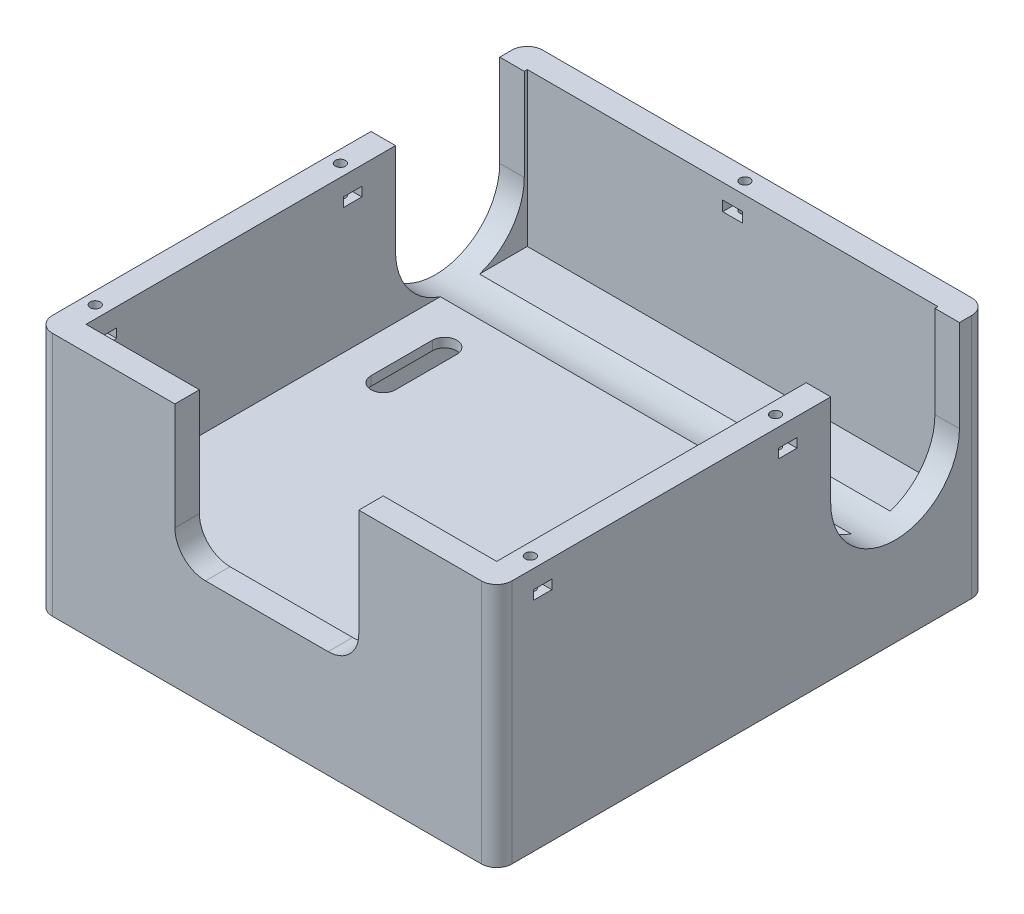
SolidWorks part; units mm, degrees
ref_plane "前视基准面" through (0, 0, 0) normal (0, 0, 1) x (1, 0, 0)
ref_plane "上视基准面" through (0, 0, 0) normal (0, 1, 0) x (1, 0, 0)
ref_plane "右视基准面" through (0, 0, 0) normal (1, 0, 0) x (0, 0, -1)
sketch "草图1" plane through (0, 0, 0) normal (0, 1, 0) x (1, 0, 0)
  line L1 (-75, 80) -> (75, 80)
  line L2 (-75, 80) -> (-75, -80)
  line L3 (-75, -80) -> (75, -80)
  line L4 (75, 80) -> (75, -80)
  line L5 (-75, 80) -> (75, -80) construction
  line L6 (-75, -80) -> (75, 80) construction
  point P0 (0, 0)
  dimension "D1" = 150
  dimension "D2" = 160
extrude "凸台-拉伸1" add sketch "草图1" along normal blind 80
sketch "草图2" plane through (-75, 0, 0) normal (-1, 0, 0) x (0, 0, 1)
  line L0 (-80, 80) -> (-80, 0) construction
  line L1 (-29, 50) -> (-29, 80)
  line L2 (-80, 80) -> (80, 80) construction
  line L3 (-29, 80) -> (-71, 80)
  line L4 (-71, 80) -> (-71, 50)
  arc A0 (-71, 50) -> (-29, 50) centre (-50, 50) ccw
  dimension "D1" = 42
  dimension "D2" = 30
  dimension "D3" = 30
extrude "切除-拉伸1" cut sketch "草图2" against normal through all
fillet "圆角1" radius 5 4 edges at (75, 40, -80) (-75, 40, -80) (75, 40, 80) (-75, 40, 80)
sketch "草图3" plane through (0, 0, 0) normal (0, -1, 0) x (1, 0, 0)
  line L0 (-70, 80) -> (70, 80) construction
  line L1 (67, 76) -> (-67, 76)
  line L2 (67, 76) -> (67, -76)
  line L3 (67, -76) -> (-67, -76)
  line L4 (-67, 76) -> (-67, -76)
  line L5 (67, 76) -> (-67, -76) construction
  line L6 (67, -76) -> (-67, 76) construction
  line L7 (75, 75) -> (75, -75) construction
  point P0 (0, 0)
  dimension "D1" = 4
  dimension "D2" = 8
extrude "切除-拉伸2" cut sketch "草图3" against normal blind 27
sketch "草图4" plane through (0, 80, 0) normal (0, 1, 0) x (1, 0, 0)
  line L0 (-70, -80) -> (70, -80) construction
  line L1 (-67, -72) -> (67, -72)
  line L2 (-67, -72) -> (-67, 72)
  line L3 (-67, 72) -> (67, 72)
  line L4 (67, -72) -> (67, 72)
  line L5 (-67, -72) -> (67, 72) construction
  line L6 (-67, 72) -> (67, -72) construction
  line L7 (-75, 29) -> (-75, -75) construction
  point P0 (0, 0)
  dimension "D1" = 8
  dimension "D2" = 8
extrude "切除-拉伸3" cut sketch "草图4" against normal blind 50
sketch "草图5" plane through (0, 0, 80) normal (0, 0, 1) x (1, 0, 0)
  line L0 (-70, 80) -> (70, 80) construction
  line L1 (30, 35) -> (-30, 35)
  line L2 (30, 35) -> (30, 80)
  line L3 (30, 80) -> (-30, 80)
  line L4 (-30, 35) -> (-30, 80)
  line L5 (30, 35) -> (-30, 80) construction
  line L6 (30, 80) -> (-30, 35) construction
  point P0 (0, 57.5)
  dimension "D1" = 45
  dimension "D2" = 60
extrude "切除-拉伸4" cut sketch "草图5" against normal blind 50
fillet "圆角2" radius 2 4 edges at (67, 13.5, 76) (67, 13.5, -76) (-67, 13.5, -76) (-67, 13.5, 76)
sketch "草图7" plane through (0, 80, 0) normal (0, 1, 0) x (1, 0, 0)
  line L0 (-60.2447, 0) -> (0, 0) construction
  line L1 (0, 0) -> (0, 114.0936) construction
  line L2 (-67, 29) -> (-67, -72) construction
  line L3 (71, 15) -> (-71, 15) construction
  line L4 (71, 15) -> (71, -65) construction
  line L5 (71, -65) -> (-71, -65) construction
  line L6 (-71, 15) -> (-71, -65) construction
  line L7 (71, 15) -> (-71, -65) construction
  line L8 (71, -65) -> (-71, 15) construction
  circle A0 centre (-71, -65) radius 1.65
  circle A1 centre (-71, 15) radius 1.65
  circle A2 centre (71, -65) radius 1.65
  circle A3 centre (71, 15) radius 1.65
  point P3 (0, -25)
  dimension "D4" = 3.3
  dimension "D5" = 3.3
  dimension "D6" = 3.3
  dimension "D7" = 3.3
  dimension "D1" = 142
  dimension "D2" = 25
  dimension "D3" = 80
  dimension "D8" = 67
extrude "切除-拉伸6" cut sketch "草图7" against normal blind 15
sketch "草图9" plane through (-75, 0, 0) normal (-1, 0, 0) x (0, 0, 1)
  line L0 (80, 80) -> (80, 0) construction
  line L1 (68, 71) -> (62, 71)
  line L2 (68, 71) -> (68, 74)
  line L3 (68, 74) -> (62, 74)
  line L4 (62, 71) -> (62, 74)
  line L5 (68, 71) -> (62, 74) construction
  line L6 (68, 74) -> (62, 71) construction
  line L7 (-29, 80) -> (75, 80) construction
  line L8 (-12, 71) -> (-18, 71)
  line L9 (-12, 71) -> (-12, 74)
  line L10 (-12, 74) -> (-18, 74)
  line L11 (-18, 71) -> (-18, 74)
  line L12 (-12, 71) -> (-18, 74) construction
  line L13 (-12, 74) -> (-18, 71) construction
  point P0 (65, 72.5)
  point P9 (-15, 72.5)
  dimension "D1" = 15
  dimension "D2" = 6
  dimension "D3" = 3
  dimension "D4" = 6
  dimension "D5" = 6
  dimension "D6" = 3
  dimension "D7" = 80
  dimension "D8" = 6
extrude "切除-拉伸7" cut sketch "草图9" against normal through all
sketch "草图11" plane through (0, 80, 0) normal (0, 1, 0) x (1, 0, 0)
  line L0 (70, 80) -> (-70, 80) construction
  circle A0 centre (0, 76) radius 1.65
  dimension "D1" = 3.3
  dimension "D2" = 4
extrude "切除-拉伸8" cut sketch "草图11" against normal blind 15
sketch "草图12" plane through (0, 0, -80) normal (0, 0, -1) x (-1, 0, 0)
  line L0 (0, 0) -> (0, 95.539) construction
  line L1 (-70, 80) -> (70, 80) construction
  line L2 (3.25, 71.7) -> (-3.25, 71.7)
  line L3 (3.25, 71.7) -> (3.25, 75)
  line L4 (3.25, 75) -> (-3.25, 75)
  line L5 (-3.25, 71.7) -> (-3.25, 75)
  line L6 (3.25, 71.7) -> (-3.25, 75) construction
  line L7 (3.25, 75) -> (-3.25, 71.7) construction
  point P3 (0, 73.35)
  dimension "D2" = 3.3
  dimension "D1" = 6.5
  dimension "D3" = 5
extrude "切除-拉伸9" cut sketch "草图12" against normal blind 15
fillet "圆角3" radius 10 2 edges at (-30, 35, 76) (30, 35, 76)
sketch "草图13" plane through (0, 27, 0) normal (0, -1, 0) x (1, 0, 0)
  line L0 (52, -10) -> (52, -30) construction
  line L1 (56, -10) -> (56, -30)
  line L2 (48, -10) -> (48, -30)
  line L3 (0, 0) -> (0, -120.711) construction
  line L4 (-52, -10) -> (-52, -30) construction
  line L5 (-56, -10) -> (-56, -30)
  line L6 (-48, -10) -> (-48, -30)
  arc A0 (56, -10) -> (48, -10) centre (52, -10) ccw
  arc A1 (48, -30) -> (56, -30) centre (52, -30) ccw
  arc A2 (-56, -10) -> (-48, -10) centre (-52, -10) cw
  arc A3 (-48, -30) -> (-56, -30) centre (-52, -30) cw
  point P2 (52, -20)
  point P12 (-52, -20)
  dimension "D2" = 4
  dimension "D1" = 20
  dimension "D3" = 20
  dimension "D4" = 52
extrude "切除-拉伸10" cut sketch "草图13" against normal through all
